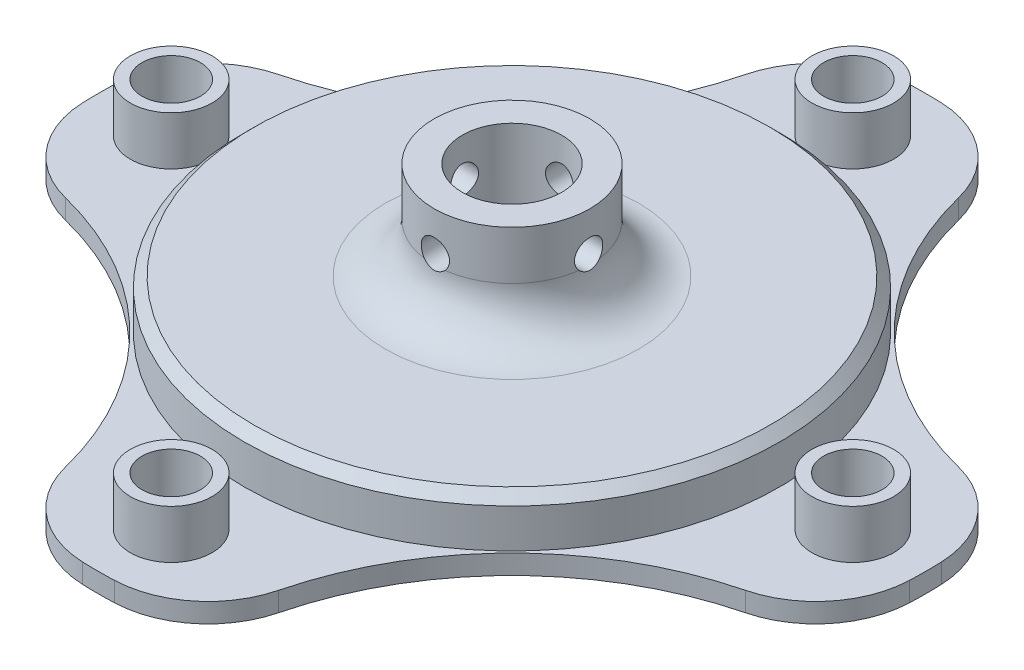
SolidWorks part; units mm, degrees
ref_plane "Front Plane" through (0, 0, 0) normal (0, 0, 1) x (1, 0, 0)
ref_plane "Top Plane" through (0, 0, 0) normal (0, 1, 0) x (1, 0, 0)
ref_plane "Right Plane" through (0, 0, 0) normal (1, 0, 0) x (0, 0, -1)
sketch "Sketch1" plane through (0, 0, 0) normal (0, 1, 0) x (1, 0, 0)
  circle A0 centre (0, 0) radius 27.5
  dimension "D1" = 55
extrude "Boss-Extrude1" add sketch "Sketch1" against normal blind 5
sketch "Sketch2" plane through (0, -5, 0) normal (0, -1, 0) x (1, 0, 0)
  circle A0 centre (0, 0) radius 42.5
  dimension "D1" = 85
extrude "Boss-Extrude2" add sketch "Sketch2" along normal blind 2
sketch "Sketch3" plane through (0, -5, 0) normal (0, 1, 0) x (1, 0, 0)
  circle A0 centre (0, 35) radius 3
  circle A1 centre (35, 0) radius 3
  circle A2 centre (0, -35) radius 3
  circle A3 centre (-35, 0) radius 3
  circle A4 centre (0, 0) radius 42.5 construction
  arc A5 (-10, 41.3068) -> (-41.3068, 10) centre (-42.9586, 42.9586) cw
  arc A6 (41.3068, 10) -> (10, 41.3068) centre (42.9586, 42.9586) cw
  arc A7 (10, -41.3068) -> (41.3068, -10) centre (42.9586, -42.9586) cw
  arc A8 (-41.3068, -10) -> (-10, -41.3068) centre (-42.9586, -42.9586) cw
  circle A10 centre (0, 0) radius 42.5
  circle A11 centre (0, 0) radius 42.5
  point P12 (0, 0)
  point P27 (0, 0)
  circle M3 centre (0, 0) radius 42.5
  dimension "D1" = 6
  dimension "D6" = 33
  dimension "D2" = 35
  dimension "D3" = 4
  dimension "D4" = 10
  dimension "D5" = 10
  dimension "D8" = 0
  dimension "D7" = 4
extrude "Cut-Extrude1" cut sketch "Sketch3" against normal blind 2 contours A5 M3 | A0 | A6 M3 | A1 | A2 | A7 M3 | A8 M3 | A3
sketch "Sketch4" plane through (0, 0, 0) normal (0, 1, 0) x (1, 0, 0)
  circle A0 centre (0, 0) radius 11.6
  circle A1 centre (0, 23.5) radius 2.5
  circle A2 centre (20.3516, 11.75) radius 2.5
  circle A3 centre (20.3516, -11.75) radius 2.5
  circle A4 centre (0, -23.5) radius 2.5
  circle A5 centre (-20.3516, -11.75) radius 2.5
  circle A6 centre (-20.3516, 11.75) radius 2.5
  point P18 (0, 0)
  dimension "D1" = 23.2
  dimension "D2" = 5
  dimension "D3" = 23.5
  dimension "D4" = 6
extrude "Cut-Extrude2" [suppressed] cut sketch "Sketch4" against normal through all
sketch "Sketch5" plane through (0, 0, 0) normal (0, 1, 0) x (1, 0, 0)
  line L0 (-17.6947, 16.2142) -> (-10.3219, 9.4583)
  line L1 (-5.1946, 23.4311) -> (-3.0302, 13.6681)
  line L2 (0, 23.537) -> (0, 0) construction
  line L3 (17.6947, 16.2142) -> (10.3219, 9.4583)
  line L4 (5.1946, 23.4311) -> (3.0302, 13.6681)
  line L5 (22.8892, -7.2169) -> (13.352, -4.2099)
  line L6 (22.8892, 7.2169) -> (13.352, 4.2099)
  line L7 (5.1946, -23.4311) -> (3.0302, -13.6681)
  line L8 (17.6947, -16.2142) -> (10.3219, -9.4583)
  line L9 (-17.6947, -16.2142) -> (-10.3219, -9.4583)
  line L10 (-5.1946, -23.4311) -> (-3.0302, -13.6681)
  line L11 (-22.8892, 7.2169) -> (-13.352, 4.2099)
  line L12 (-22.8892, -7.2169) -> (-13.352, -4.2099)
  arc A0 (-10.3219, 9.4583) -> (-3.0302, 13.6681) centre (0, 0) cw
  arc A1 (-17.6947, 16.2142) -> (-5.1946, 23.4311) centre (0, 0) cw
  arc A2 (5.1946, 23.4311) -> (17.6947, 16.2142) centre (0, 0) cw
  arc A3 (3.0302, 13.6681) -> (10.3219, 9.4583) centre (0, 0) cw
  arc A4 (22.8892, 7.2169) -> (22.8892, -7.2169) centre (0, 0) cw
  arc A5 (13.352, 4.2099) -> (13.352, -4.2099) centre (0, 0) cw
  arc A6 (17.6947, -16.2142) -> (5.1946, -23.4311) centre (0, 0) cw
  arc A7 (10.3219, -9.4583) -> (3.0302, -13.6681) centre (0, 0) cw
  arc A8 (-5.1946, -23.4311) -> (-17.6947, -16.2142) centre (0, 0) cw
  arc A9 (-3.0302, -13.6681) -> (-10.3219, -9.4583) centre (0, 0) cw
  arc A10 (-22.8892, -7.2169) -> (-22.8892, 7.2169) centre (0, 0) cw
  arc A11 (-13.352, -4.2099) -> (-13.352, 4.2099) centre (0, 0) cw
  point P30 (0, 0)
  dimension "D2" = 14
  dimension "D3" = 35
  dimension "D4" = 12.5
  dimension "D1" = 10
  dimension "D5" = 6
extrude "Cut-Extrude3" [suppressed] cut sketch "Sketch5" against normal through all
fillet "Fillet1" radius 10 8 edges at (41.3068, -6, -10) (10, -6, -41.3068) (-10, -6, -41.3068) (-41.3068, -6, -10) (-41.3068, -6, 10) (-10, -6, 41.3068) (10, -6, 41.3068) (41.3068, -6, 10)
sketch "Sketch6" plane through (0, 0, 0) normal (0, 1, 0) x (1, 0, 0)
  circle A0 centre (0, 0) radius 8
  dimension "D1" = 16
extrude "Boss-Extrude3" add sketch "Sketch6" along normal blind 10
fillet "Fillet2" radius 5 1 edges at (0, 0, 8)
sketch "Sketch7" plane through (0, 10, 0) normal (0, 1, 0) x (1, 0, 0)
  circle A0 centre (0, 0) radius 5.1
  dimension "D1" = 10.2
extrude "Cut-Extrude4" cut sketch "Sketch7" against normal blind 20
sketch "Sketch10" plane through (0, 0, 0) normal (0, 0, 1) x (1, 0, 0)
  circle A0 centre (0, 6) radius 1.45
  point P2 (0, 0)
  dimension "D1" = 2.9
  dimension "D2" = 6
extrude "Cut-Extrude5" cut sketch "Sketch10" along normal through all both and the other way through all
pattern_circular "CirPattern1" count 4 over 360 about axis through (0, 10, 0) along (0, -1, 0) of "Cut-Extrude5"
chamfer "Chamfer1" distance 1 angle 45 1 edges at (0, 0, 27.5)
sketch "Sketch11" plane through (0, -5, 0) normal (0, 1, 0) x (1, 0, 0)
  circle A0 centre (0, -35) radius 3 construction
  circle A1 centre (35, 0) radius 3 construction
  circle A2 centre (0, 35) radius 3 construction
  circle A3 centre (-35, 0) radius 3 construction
  circle A4 centre (0, -35) radius 3
  circle A5 centre (35, 0) radius 3
  circle A6 centre (0, 35) radius 3
  circle A7 centre (-35, 0) radius 3
  circle A8 centre (0, -35) radius 4.2
  circle A9 centre (35, 0) radius 4.2
  circle A10 centre (0, 35) radius 4.2
  circle A11 centre (-35, 0) radius 4.2
  dimension "D1" = 1.2
extrude "Boss-Extrude4" add sketch "Sketch11" along normal blind 5
